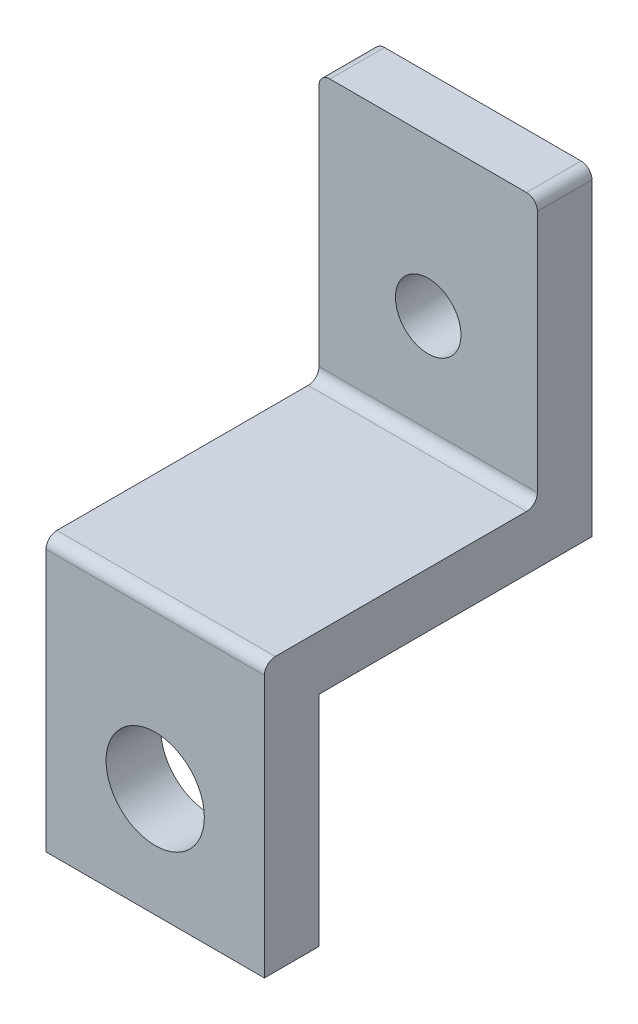
SolidWorks part; units mm, degrees
material "6061 Alloy"
ref_plane "前视基准面" through (0, 0, 0) normal (0, 0, 1) x (1, 0, 0)
ref_plane "上视基准面" through (0, 0, 0) normal (0, 1, 0) x (1, 0, 0)
ref_plane "右视基准面" through (0, 0, 0) normal (1, 0, 0) x (0, 0, -1)
other "Configuration Table"
sketch "Sketch1" plane through (0, 0, 0) normal (0, 0, 1) x (1, 0, 0)
  line L0 (0, 0) -> (0, 30) construction
  line L2 (-10, 10) -> (-10, -10)
  line L3 (-10, -10) -> (10, -10)
  line L4 (10, 10) -> (10, -10)
  line L5 (-10, 10) -> (10, -10) construction
  line L6 (-10, -10) -> (10, 10) construction
  line L7 (0, 30) -> (0, 45) construction
  line L8 (0, 45) -> (0, 49) construction
  line L9 (0, 49) -> (-10, 49) construction
  line L10 (-10, 39.3) -> (-10, 10)
  line L11 (10, 39.3) -> (10, 10)
  line L12 (10, -10) -> (10, 39.3) construction
  line L13 (10, 39.3) -> (-10, 39.3)
  line L14 (-10, 49) -> (-10, 39.3) construction
  line L15 (10, 49) -> (0, 49) construction
  line L16 (10, 49) -> (10, 39.3) construction
  circle A0 centre (0, 0) radius 4.5
  circle A1 centre (0, 30) radius 3 construction
  circle A2 centre (0, 45) radius 2.5 construction
  dimension "D1" = 20
  dimension "D3" = 9
  dimension "D5" = 6
  dimension "D7" = 5
  dimension "D2" = 20
  dimension "D4" = 30
  dimension "D6" = 15
  dimension "D8" = 4
  dimension "D9" = 49.3
extrude "Boss-Extrude1" add sketch "Sketch1" along normal blind 5
sketch "Sketch2" plane through (0, 0, 0) normal (0, 0, -1) x (-1, 0, 0)
  line L0 (-10, 39.3) -> (10, 39.3) construction
  line L1 (-10, -10) -> (10, -10) construction
  line L2 (-10, -10) -> (-10, 10) construction
  line L3 (-10, 10) -> (10, 10) construction
  line L4 (10, -10) -> (10, 10) construction
  line L5 (-10, -10) -> (10, 10) construction
  line L6 (-10, 10) -> (10, -10) construction
  line L7 (-10, 39.3) -> (10, 39.3)
  line L8 (-10, 39.3) -> (-10, 10)
  line L9 (-10, 10) -> (10, 10)
  line L10 (10, 39.3) -> (10, 10)
  line L11 (-10, 39.3) -> (10, 39.3) construction
  point P0 (0, 0)
  dimension "D1" = 20
  dimension "D2" = 20
extrude "Boss-Extrude2" add sketch "Sketch2" along normal blind 25
sketch "Sketch3" plane through (10, 0, 0) normal (1, 0, 0) x (0, 0, -1)
  line L0 (0, 10) -> (0, 15) construction
  line L1 (0, 15) -> (-5, 15)
  line L2 (-5, -10) -> (-5, 39.3) construction
  line L3 (-5, 15) -> (-5, 39.3)
  line L6 (20, 39.3) -> (20, 15)
  line L7 (20, 15) -> (0, 15)
  line L8 (-5, 39.3) -> (20, 39.3)
  line L9 (-5, 39.3) -> (25, 39.3) construction
  dimension "D1" = 5
extrude "Cut-Extrude1" cut sketch "Sketch3" against normal blind 30
sketch "Sketch4" plane through (0, 0, -20) normal (0, 0, 1) x (1, 0, 0)
  line L0 (0, 15) -> (0, 25) construction
  line L1 (-10, 15) -> (10, 15) construction
  circle A0 centre (0, 45) radius 2.5
  circle A1 centre (0, 30) radius 3 construction
  circle A2 centre (0, 25) radius 3
  dimension "D2" = 6
  dimension "D1" = 10
extrude "Cut-Extrude2" cut sketch "Sketch4" against normal blind 30
fillet "Fillet2" radius 1 4 edges at (0, 15, 5) (10, 39.3, -22.5) (-10, 39.3, -22.5) (0, 15, -20)
mirror "Mirror1" [suppressed]
delete or keep bodies "Body-Delete/Keep 1" [suppressed] type delete bodies bodies 109
